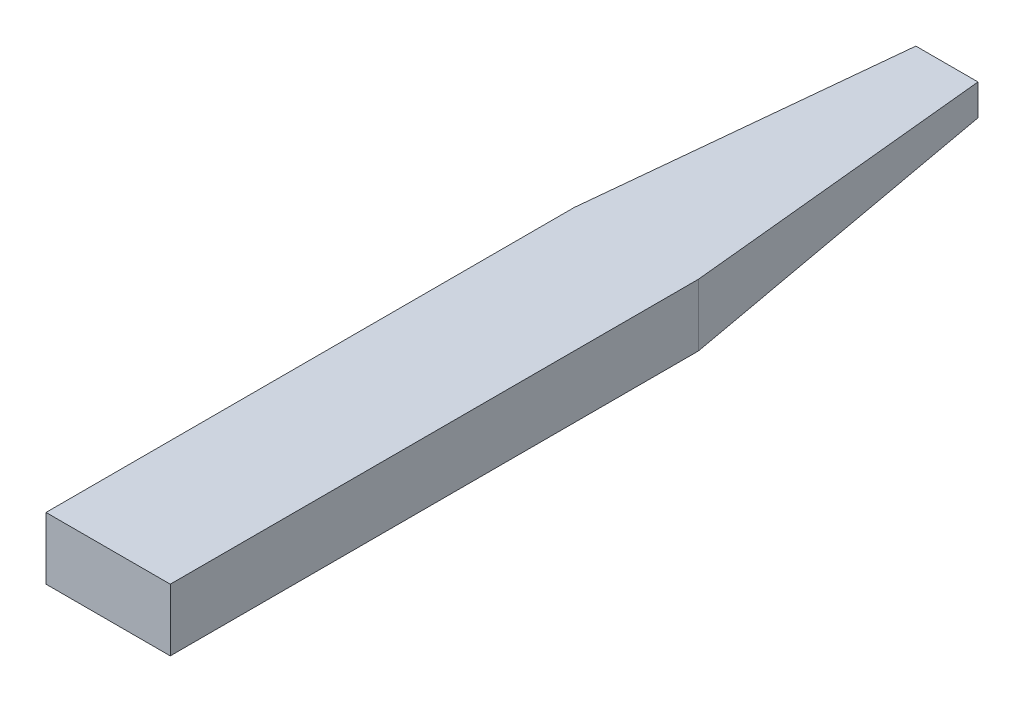
SolidWorks part; units mm, degrees
ref_plane "Front Plane" through (0, 0, 0) normal (0, 0, 1) x (1, 0, 0)
ref_plane "Top Plane" through (0, 0, 0) normal (0, 1, 0) x (1, 0, 0)
ref_plane "Right Plane" through (0, 0, 0) normal (1, 0, 0) x (0, 0, -1)
sketch "Sketch1" plane through (0, 0, 0) normal (0, 0, 1) x (1, 0, 0)
  line L1 (0, 0) -> (101.6, 0)
  line L2 (0, 0) -> (0, 50.8)
  line L3 (0, 50.8) -> (101.6, 50.8)
  line L4 (101.6, 0) -> (101.6, 50.8)
  dimension "D1" = 101.6
  dimension "D2" = 50.8
extrude "Boss-Extrude1" add sketch "Sketch1" along normal blind 431.8
ref_plane "Plane1" through (0, 25.4, 0) normal (0, 1, 0) x (1, 0, 0)
ref_plane "Plane2" through (50.8, 0, 0) normal (-1, 0, 0) x (0, 0, 1)
ref_plane "Plane3" through (0, 0, 431.8) normal (0, 0, 1) x (1, 0, 0)
sketch "Sketch2" plane through (0, 0, 0) normal (0, 0, 1) x (1, 0, 0)
  line L1 (0, 0) -> (101.6, 0)
  line L2 (0, 0) -> (0, 50.8)
  line L3 (0, 50.8) -> (101.6, 50.8)
  line L4 (101.6, 0) -> (101.6, 50.8)
  dimension "D1" = 50.8
  dimension "D2" = 101.6
ref_plane "Plane4" through (0, 0, -254) normal (0, 0, -1) x (-1, 0, 0)
sketch "Sketch3" plane through (0, 0, -254) normal (0, 0, -1) x (-1, 0, 0)
  line L1 (-76.2, 25.4) -> (-25.4, 25.4)
  line L2 (-76.2, 25.4) -> (-76.2, 50.8)
  line L3 (-76.2, 50.8) -> (-25.4, 50.8)
  line L4 (-25.4, 25.4) -> (-25.4, 50.8)
  dimension "D1" = 25.4
  dimension "D2" = 50.8
  dimension "D3" = 25.4
  dimension "D4" = 25.4
loft "Loft1" add profiles "Sketch2", "Sketch3"
ref_plane "Plane5" through (0, 38.1, 0) normal (0, 1, 0) x (1, 0, 0)
